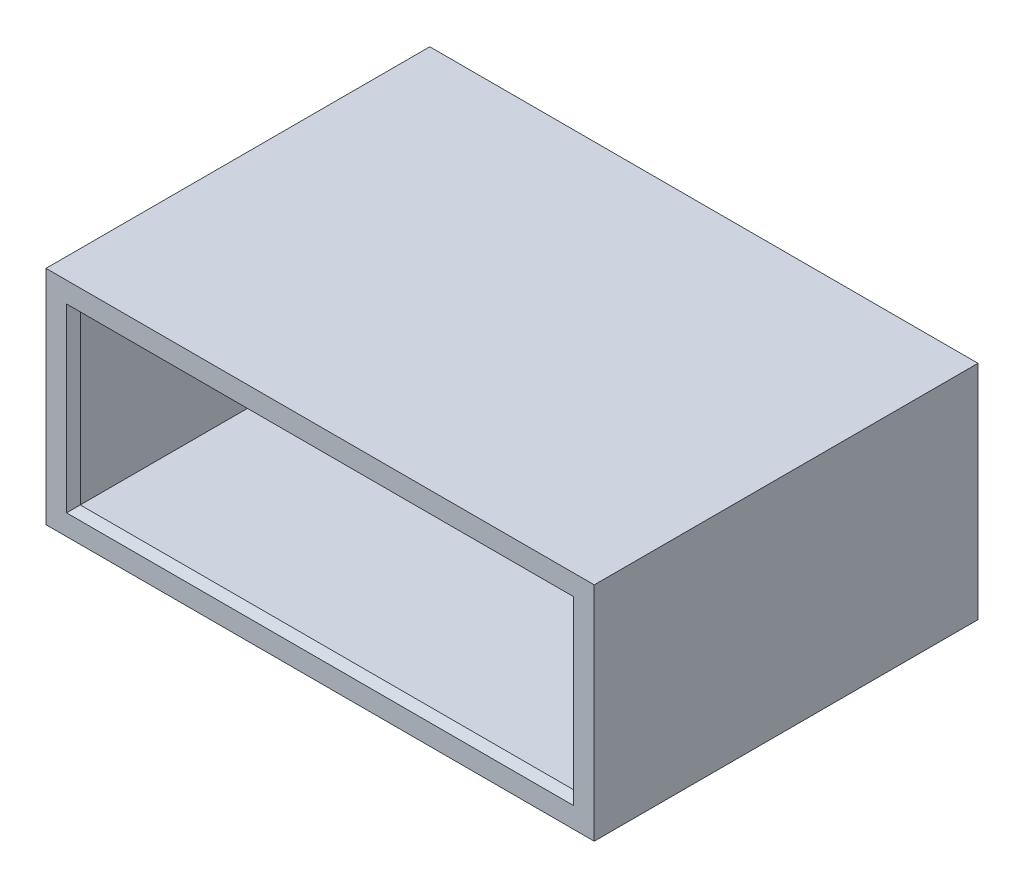
SolidWorks part; units mm, degrees
ref_plane "Front Plane" through (0, 0, 0) normal (0, 0, 1) x (1, 0, 0)
ref_plane "Top Plane" through (0, 0, 0) normal (0, 1, 0) x (1, 0, 0)
ref_plane "Right Plane" through (0, 0, 0) normal (1, 0, 0) x (0, 0, -1)
sketch "Sketch1" plane through (0, 0, 0) normal (0, 0, 1) x (1, 0, 0)
  line L5 (-9, -3.05) -> (9, -3.05)
  line L6 (-9, -3.05) -> (-9, 3.05)
  line L7 (-9, 3.05) -> (9, 3.05)
  line L8 (9, -3.05) -> (9, 3.05)
  line L9 (-9, -3.05) -> (9, 3.05) construction
  line L10 (-9, 3.05) -> (9, -3.05) construction
  line L11 (-10, -4.05) -> (10, -4.05)
  line L12 (-10, -4.05) -> (-10, 4.05)
  line L13 (-10, 4.05) -> (10, 4.05)
  line L14 (10, -4.05) -> (10, 4.05)
  line L15 (-10, -4.05) -> (10, 4.05) construction
  line L16 (-10, 4.05) -> (10, -4.05) construction
  point P0 (0, 0)
  point P5 (0, 0)
  dimension "D1" = 18
  dimension "D2" = 6.1
  dimension "D3" = 20
  dimension "D4" = 1
extrude "Boss-Extrude1" add sketch "Sketch1" along normal blind 14
chamfer "Chamfer1" distance 0.25 angle 45 8 edges at (0, 3.05, 14) (-9, 0, 14) (0, -3.05, 14) (9, 0, 14) (-9, 0, 0) (0, 3.05, 0) (9, 0, 0) (0, -3.05, 0)
